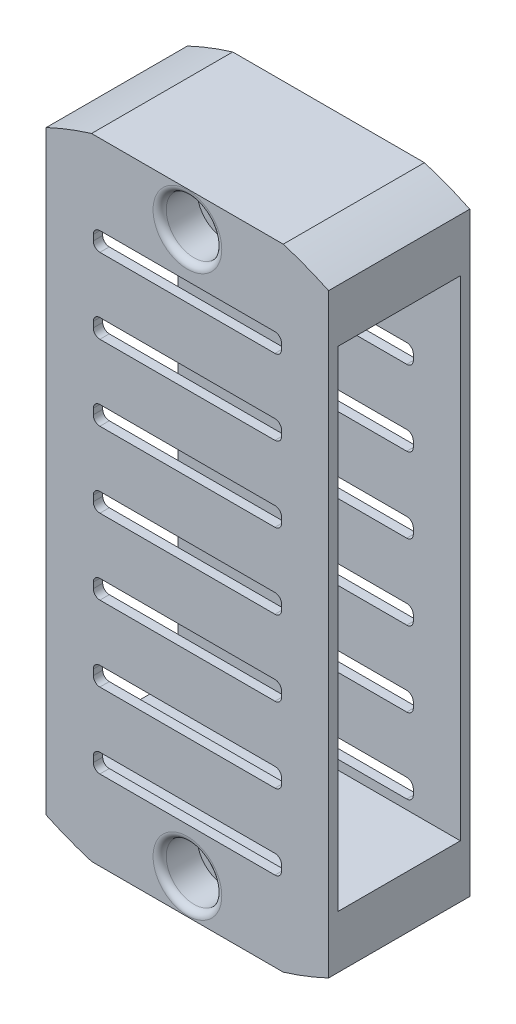
SolidWorks part; units mm, degrees
ref_plane "Front Plane" through (0, 0, 0) normal (0, 0, 1) x (1, 0, 0)
ref_plane "Top Plane" through (0, 0, 0) normal (0, 1, 0) x (1, 0, 0)
ref_plane "Right Plane" through (0, 0, 0) normal (1, 0, 0) x (0, 0, -1)
sketch "Sketch1" plane through (0, 0, 0) normal (0, 0, 1) x (1, 0, 0)
  line L0 (10.1263, 67.193) -> (10.1263, -0.293) construction
  line L3 (-4.8737, 33.45) -> (-4.8737, 46.45) construction
  line L4 (-4.8737, 46.45) -> (25.1263, 46.45) construction
  line L5 (-4.8737, 46.45) -> (-4.8737, 59.45) construction
  line L6 (-4.8737, 59.45) -> (25.1263, 59.45) construction
  line L7 (25.1263, 46.45) -> (25.1263, 59.45) construction
  line L10 (-4.8737, 46.45) -> (25.1263, 46.45) construction
  line L11 (-4.8737, 33.45) -> (25.1263, 33.45) construction
  line L12 (25.1263, 33.45) -> (25.1263, 46.45) construction
  line L13 (-4.8737, 20.45) -> (-4.8737, 33.45) construction
  line L14 (-4.8737, 33.45) -> (25.1263, 33.45) construction
  line L15 (-4.8737, 20.45) -> (25.1263, 20.45) construction
  line L16 (25.1263, 20.45) -> (25.1263, 33.45) construction
  line L17 (-4.8737, 7.45) -> (-4.8737, 20.45) construction
  line L18 (-4.8737, 20.45) -> (25.1263, 20.45) construction
  line L19 (-4.8737, 7.45) -> (25.1263, 7.45)
  line L20 (25.1263, 7.45) -> (25.1263, 20.45) construction
  line L21 (-4.8737, 46.45) -> (-4.8737, 33.45) construction
  line L22 (-25.1503, 33.45) -> (45.3331, 33.45) construction
  line L23 (-4.8737, 59.45) -> (25.1263, 7.45) construction
  line L28 (25.1263, 59.45) -> (-4.8737, 7.45) construction
  line L29 (20.3496, 67.193) -> (-0.097, 67.193) construction
  line L30 (20.3123, 66.943) -> (-0.06, 66.943)
  line L31 (-4.8737, 59.45) -> (25.1263, 59.45)
  line L32 (-4.8737, 59.45) -> (-4.8737, 65.0852)
  line L33 (25.1263, 59.45) -> (25.1263, 65.0733)
  line L34 (-4.8737, 7.45) -> (25.1263, 7.45)
  line L35 (25.1263, 7.45) -> (25.1263, 1.8267)
  line L36 (20.3123, -0.043) -> (-0.06, -0.043)
  line L37 (-4.8737, 7.45) -> (-4.8737, 1.8148)
  arc A0 (45.0831, 33.4501) -> (20.3123, 66.943) centre (10.0815, 33.47) ccw construction
  arc A1 (25.1263, 1.8267) -> (20.3123, -0.043) centre (10.0815, 33.43) cw
  arc A4 (45.3331, 33.45) -> (20.3496, 67.193) centre (10.0815, 33.47) ccw construction
  arc A6 (-0.097, 67.193) -> (-25.1503, 33.45) centre (10.1013, 33.4489) ccw construction
  arc A7 (25.1263, 65.0733) -> (20.3123, 66.943) centre (10.0815, 33.47) ccw
  arc A8 (-0.06, 66.943) -> (-4.8737, 65.0852) centre (10.1013, 33.4489) ccw
  arc A9 (-0.06, 66.943) -> (-24.9003, 33.45) centre (10.1013, 33.4489) ccw construction
  arc A10 (-0.06, -0.043) -> (-4.8737, 1.8148) centre (10.1013, 33.4512) cw
  point P6 (10.1263, 52.95)
  point P11 (10.1263, 33.45)
  point P12 (10.1263, 33.45)
  dimension "D1" = 13
  dimension "D2" = 30
  dimension "D4" = 13
  dimension "D5" = 0.25
  dimension "D6" = 0
  dimension "D7" = 20.4466
  dimension "D3" = 4
extrude "Boss-Extrude1" add sketch "Sketch1" along normal blind 13 separate body
sketch "Sketch2" plane through (0, 0, 13) normal (0, 0, 1) x (1, 0, 0)
  line L0 (-4.8737, 7.45) -> (-4.8737, 1.8148) construction
  line L1 (20.3123, -0.043) -> (-0.06, -0.043) construction
  line L2 (25.1263, 7.45) -> (25.1263, 1.8267) construction
  line L3 (-4.8737, 59.45) -> (-4.8737, 65.0852) construction
  line L4 (20.3123, 66.943) -> (-0.06, 66.943) construction
  line L5 (25.1263, 59.45) -> (25.1263, 65.0733) construction
  line L6 (-4.8737, 7.45) -> (-4.8737, 1.8148)
  line L7 (20.3123, -0.043) -> (-0.06, -0.043)
  line L8 (25.1263, 7.45) -> (25.1263, 1.8267)
  line L9 (-4.8737, 59.45) -> (-4.8737, 65.0852)
  line L10 (20.3123, 66.943) -> (-0.06, 66.943)
  line L11 (25.1263, 59.45) -> (25.1263, 65.0733)
  line L12 (25.1263, 59.45) -> (25.1263, 7.45)
  line L13 (-4.8737, 59.45) -> (-4.8737, 7.45)
  arc A0 (-4.8737, 1.8148) -> (-0.06, -0.043) centre (10.1013, 33.4512) ccw construction
  arc A1 (20.3123, -0.043) -> (25.1263, 1.8267) centre (10.0815, 33.43) ccw construction
  arc A2 (-0.06, 66.943) -> (-4.8737, 65.0852) centre (10.1013, 33.4489) ccw construction
  arc A3 (25.1263, 65.0733) -> (20.3123, 66.943) centre (10.0815, 33.47) ccw construction
  arc A4 (-4.8737, 1.8148) -> (-0.06, -0.043) centre (10.1013, 33.4512) ccw
  arc A5 (20.3123, -0.043) -> (25.1263, 1.8267) centre (10.0815, 33.43) ccw
  arc A6 (-0.06, 66.943) -> (-4.8737, 65.0852) centre (10.1013, 33.4489) ccw
  arc A7 (25.1263, 65.0733) -> (20.3123, 66.943) centre (10.0815, 33.47) ccw
extrude "Boss-Extrude2" add sketch "Sketch2" along normal blind 1
ref_plane "Plane1" through (0, 0, 6.5) normal (0, 0, -1) x (-1, 0, 0)
mirror "Mirror1" about plane through (0, 0, 6.5) normal (0, 0, -1) of "Boss-Extrude2"
sketch "Sketch3" plane through (0, 0, 14) normal (0, 0, 1) x (1, 0, 0)
  line L0 (-4.8737, 7.45) -> (25.1263, 7.45) construction
  line L1 (-4.8737, 7.45) -> (25.1263, 7.45) construction
  line L2 (-4.8737, 59.45) -> (25.1263, 59.45) construction
  line L3 (-4.8737, 59.45) -> (25.1263, 59.45) construction
  line L4 (-4.8737, 33.45) -> (25.1263, 33.45) construction
  line L5 (-4.8737, 65.0852) -> (-4.8737, 1.8148) construction
  line L6 (25.1263, 1.8267) -> (25.1263, 65.0733) construction
  line L7 (19.4263, 40.45) -> (0.8263, 40.45)
  line L8 (19.4263, 32.45) -> (0.8263, 32.45)
  line L9 (20.1263, 33.15) -> (20.1263, 33.75)
  line L10 (19.4263, 34.45) -> (0.8263, 34.45)
  line L11 (0.1263, 33.15) -> (0.1263, 33.75)
  line L12 (20.1263, 32.45) -> (0.1263, 34.45) construction
  line L13 (20.1263, 34.45) -> (0.1263, 32.45) construction
  line L14 (0.1263, 41.15) -> (0.1263, 41.75)
  line L15 (19.4263, 42.45) -> (0.8263, 42.45)
  line L16 (20.1263, 41.15) -> (20.1263, 41.75)
  line L17 (19.4263, 48.45) -> (0.8263, 48.45)
  line L18 (0.1263, 49.15) -> (0.1263, 49.75)
  line L19 (19.4263, 50.45) -> (0.8263, 50.45)
  line L20 (20.1263, 49.15) -> (20.1263, 49.75)
  line L21 (19.4263, 56.45) -> (0.8263, 56.45)
  line L22 (0.1263, 57.15) -> (0.1263, 57.75)
  line L23 (19.4263, 58.45) -> (0.8263, 58.45)
  line L24 (20.1263, 57.15) -> (20.1263, 57.75)
  line L25 (19.4263, 32.45) -> (19.4263, 40.45) construction
  line L26 (19.4263, 24.45) -> (0.8263, 24.45)
  line L27 (0.1263, 25.15) -> (0.1263, 25.75)
  line L28 (19.4263, 26.45) -> (0.8263, 26.45)
  line L29 (20.1263, 25.15) -> (20.1263, 25.75)
  line L30 (19.4263, 16.45) -> (0.8263, 16.45)
  line L31 (0.1263, 17.15) -> (0.1263, 17.75)
  line L32 (19.4263, 18.45) -> (0.8263, 18.45)
  line L33 (20.1263, 17.15) -> (20.1263, 17.75)
  line L34 (19.4263, 8.45) -> (0.8263, 8.45)
  line L35 (0.1263, 9.15) -> (0.1263, 9.75)
  line L36 (19.4263, 10.45) -> (0.8263, 10.45)
  line L37 (20.1263, 9.15) -> (20.1263, 9.75)
  line L38 (19.4263, 32.45) -> (19.4263, 24.45) construction
  arc A0 (20.1263, 33.75) -> (19.4263, 34.45) centre (19.4263, 33.75) ccw
  arc A1 (19.4263, 32.45) -> (20.1263, 33.15) centre (19.4263, 33.15) ccw
  arc A2 (0.8263, 34.45) -> (0.1263, 33.75) centre (0.8263, 33.75) ccw
  arc A3 (0.8263, 32.45) -> (0.1263, 33.15) centre (0.8263, 33.15) cw
  arc A4 (0.8263, 40.45) -> (0.1263, 41.15) centre (0.8263, 41.15) cw
  arc A5 (0.8263, 42.45) -> (0.1263, 41.75) centre (0.8263, 41.75) ccw
  arc A6 (19.4263, 40.45) -> (20.1263, 41.15) centre (19.4263, 41.15) ccw
  arc A7 (20.1263, 41.75) -> (19.4263, 42.45) centre (19.4263, 41.75) ccw
  arc A8 (0.8263, 48.45) -> (0.1263, 49.15) centre (0.8263, 49.15) cw
  arc A9 (0.8263, 50.45) -> (0.1263, 49.75) centre (0.8263, 49.75) ccw
  arc A10 (19.4263, 48.45) -> (20.1263, 49.15) centre (19.4263, 49.15) ccw
  arc A11 (20.1263, 49.75) -> (19.4263, 50.45) centre (19.4263, 49.75) ccw
  arc A12 (0.8263, 56.45) -> (0.1263, 57.15) centre (0.8263, 57.15) cw
  arc A13 (0.8263, 58.45) -> (0.1263, 57.75) centre (0.8263, 57.75) ccw
  arc A14 (19.4263, 56.45) -> (20.1263, 57.15) centre (19.4263, 57.15) ccw
  arc A15 (20.1263, 57.75) -> (19.4263, 58.45) centre (19.4263, 57.75) ccw
  arc A16 (0.8263, 24.45) -> (0.1263, 25.15) centre (0.8263, 25.15) cw
  arc A17 (0.8263, 26.45) -> (0.1263, 25.75) centre (0.8263, 25.75) ccw
  arc A18 (19.4263, 24.45) -> (20.1263, 25.15) centre (19.4263, 25.15) ccw
  arc A19 (20.1263, 25.75) -> (19.4263, 26.45) centre (19.4263, 25.75) ccw
  arc A20 (0.8263, 16.45) -> (0.1263, 17.15) centre (0.8263, 17.15) cw
  arc A21 (0.8263, 18.45) -> (0.1263, 17.75) centre (0.8263, 17.75) ccw
  arc A22 (19.4263, 16.45) -> (20.1263, 17.15) centre (19.4263, 17.15) ccw
  arc A23 (20.1263, 17.75) -> (19.4263, 18.45) centre (19.4263, 17.75) ccw
  arc A24 (0.8263, 8.45) -> (0.1263, 9.15) centre (0.8263, 9.15) cw
  arc A25 (0.8263, 10.45) -> (0.1263, 9.75) centre (0.8263, 9.75) ccw
  arc A26 (19.4263, 8.45) -> (20.1263, 9.15) centre (19.4263, 9.15) ccw
  arc A27 (20.1263, 9.75) -> (19.4263, 10.45) centre (19.4263, 9.75) ccw
  point P10 (10.1263, 33.45)
  dimension "D3" = 0.7
  dimension "D1" = 20
  dimension "D2" = 2
  dimension "D5" = 8
  dimension "D7" = 8
  dimension "D4" = 4
  dimension "D6" = 4
extrude "Cut-Extrude1" cut sketch "Sketch3" against normal up to surface (15 mm away) and the other way through all up to face at (10.1263, 33.45, -1)
sketch "Sketch5" plane through (0, 0, 14) normal (0, 0, 1) x (1, 0, 0)
  line L3 (10.1262, -0.043) -> (10.1263, 7.45) construction
  line L5 (-4.8737, 7.45) -> (25.1263, 7.45) construction
  line L6 (-4.8737, 7.45) -> (25.1263, 7.45) construction
  line L7 (-0.06, -0.043) -> (20.3123, -0.043) construction
  circle A0 centre (10.1262, 3.7035) radius 1.7 construction
  circle A1 centre (10.1262, 3.7035) radius 2.95
  point P1 (10.1262, 3.7035)
  dimension "D1" = 3.4
  dimension "D2" = 1.25
  dimension "D3" = 5.9
extrude "Cut-Extrude2" cut sketch "Sketch5" against normal blind 4
sketch "Sketch6" plane through (0, 0, -1) normal (0, 0, -1) x (-1, 0, 0)
  circle A0 centre (-10.1262, 3.7035) radius 1.7 construction
  circle A1 centre (-10.1262, 3.7035) radius 1.7 construction
  circle A2 centre (-10.1262, 3.7035) radius 1.7
  dimension "D1" = 3.4
extrude "Cut-Extrude3" cut sketch "Sketch6" against normal up to surface (15 mm away) up to face at (13.0762, 3.7035, 14)
sketch "Sketch7" plane through (0, 0, -1) normal (0, 0, -1) x (-1, 0, 0)
  circle A1 centre (-10.1262, 3.7035) radius 2.95 construction
  circle A2 centre (-10.1262, 3.7035) radius 2.95
extrude "Cut-Extrude4" cut sketch "Sketch7" against normal blind 5 contours A2
ref_plane "Plane2" through (0, 33.45, 0) normal (0, -1, 0) x (-1, 0, 0)
mirror "Mirror3" about plane through (0, 33.45, 0) normal (0, -1, 0) of "Cut-Extrude4", "Cut-Extrude3", "Cut-Extrude2"
fillet "Fillet1" radius 0.7 4 edges at (7.1762, 63.1965, -1) (7.1762, 3.7035, -1) (13.0762, 3.7035, 14) (13.0762, 63.1965, 14)
